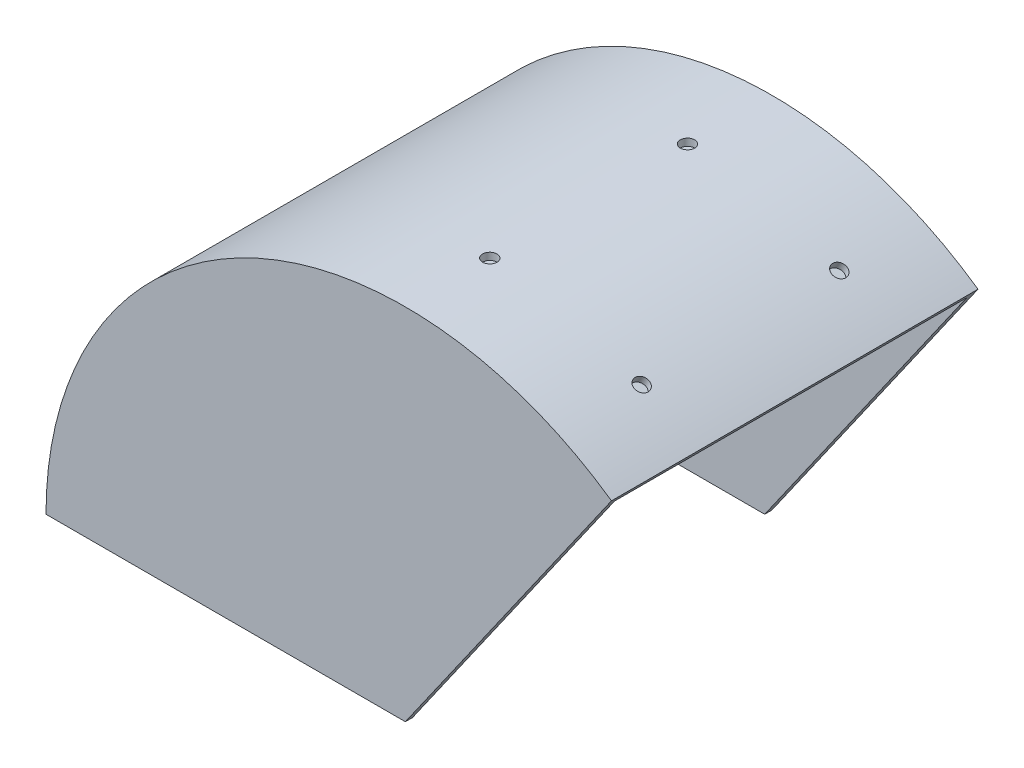
SolidWorks part; units mm, degrees
ref_plane "Front Plane" through (0, 0, 0) normal (0, 0, 1) x (1, 0, 0)
ref_plane "Top Plane" through (0, 0, 0) normal (0, 1, 0) x (1, 0, 0)
ref_plane "Right Plane" through (0, 0, 0) normal (1, 0, 0) x (0, 0, -1)
sketch "Sketch1" plane through (0, 0, 0) normal (0, 0, 1) x (1, 0, 0)
  line L0 (127, 0) -> (0, 0)
  line L1 (0, 0) -> (-127, 0)
  arc A0 (127, 0) -> (-127, 0) centre (0, 0) ccw
  point P4 (93.2609, 86.2056)
  dimension "D1" = 127
  dimension "D2" = 180
extrude "Boss-Extrude1" add sketch "Sketch1" along normal blind 129.54
ref_point "Point1"
ref_point "Point2"
ref_plane "Plane1" through (0, 127, 129.54) normal (0, 1, 0) x (1, 0, 0)
ref_plane "Plane2" through (53.6765, 115.0992, 129.54) normal (0.4226, 0.9063, 0) x (0.9063, -0.4226, 0)
sketch "Sketch2" plane through (0, 127, 129.54) normal (0, 1, 0) x (1, 0, 0)
  line L0 (0, 0) -> (0, 129.54)
  line L1 (0, 29.845) -> (0, 99.695)
  circle A0 centre (0, 29.845) radius 2.54
  circle A2 centre (0, 99.695) radius 2.54
  point P7 (0, 64.77)
  dimension "D2" = 5.08
  dimension "D1" = 69.85
extrude "Cut-Extrude1" cut sketch "Sketch2" against normal blind 2.54 contours A0 | A2
sketch "Sketch4" plane through (53.6765, 115.0992, 129.54) normal (0.4226, 0.9063, 0) x (0.9063, -0.4226, 0)
  line L0 (0, 0) -> (0, 129.54)
  line L1 (0, 29.845) -> (0, 99.695)
  circle A0 centre (0, 29.845) radius 2.54
  circle A1 centre (0, 99.695) radius 2.54
  point P7 (0, 64.77)
  dimension "D2" = 5.08
  dimension "D1" = 69.85
extrude "Cut-Extrude2" cut sketch "Sketch4" against normal blind 2.54 contours A0 | A1
sketch "Sketch5" plane through (0, 0, 129.54) normal (0, 0, 1) x (1, 0, 0)
  line L0 (0, 0) -> (72.8442, 104.0323)
  line L1 (-127, 0) -> (127, 0)
  line L2 (-127, 0) -> (127, 0)
  arc A1 (127, 0) -> (-127, 0) centre (0, 0) ccw
  arc A2 (127, 0) -> (-127, 0) centre (0, 0) ccw
  line M4 (-127, 0) -> (127, 0)
  arc M5 (127, 0) -> (-127, 0) centre (0, 0) ccw
  dimension "D2" = 55
  dimension "D1" = 0
extrude "Cut-Extrude3" cut sketch "Sketch5" against normal through all contours L0 M4 M5
shell "Shell1" thickness 2.54
